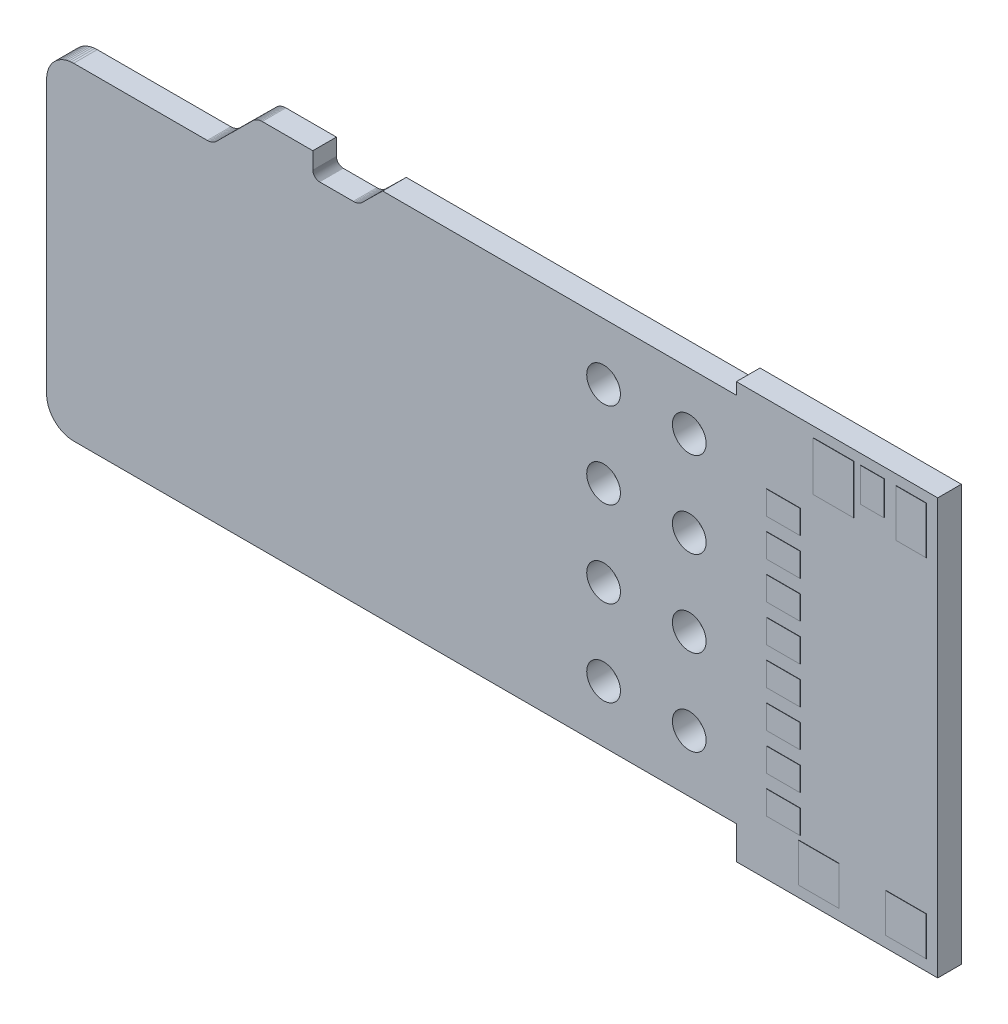
SolidWorks part; units mm, degrees
ref_plane "Front Plane" through (0, 0, 0) normal (0, 0, 1) x (1, 0, 0)
ref_plane "Top Plane" through (0, 0, 0) normal (0, 1, 0) x (1, 0, 0)
ref_plane "Right Plane" through (0, 0, 0) normal (1, 0, 0) x (0, 0, -1)
sketch "BOARD_OUTLINE" plane through (0, 0, 0) normal (0, 0, 1) x (1, 0, 0)
  line L0 (15, 5.5) -> (20.447, 5.5)
  line L1 (15, -5.5) -> (20.447, -5.5)
  line L2 (26.416, -6.477) -> (20.447, -6.477)
  line L3 (20.447, -5.5) -> (20.447, -6.477)
  line L4 (20.447, 5.85) -> (26.416, 5.85)
  line L5 (20.447, 5.85) -> (20.447, 5.5)
  line L6 (26.416, 5.85) -> (26.416, -6.477)
  line L7 (0, -4.7) -> (0, 3.4)
  line L8 (0, -4.7) -> (0.003, -4.7697)
  line L9 (0.003, -4.7697) -> (0.0122, -4.8389)
  line L10 (0.0122, -4.8389) -> (0.0273, -4.9071)
  line L11 (0.0273, -4.9071) -> (0.0482, -4.9736)
  line L12 (0.0482, -4.9736) -> (0.075, -5.0381)
  line L13 (0.075, -5.0381) -> (0.1072, -5.1)
  line L14 (0.1072, -5.1) -> (0.1447, -5.1589)
  line L15 (0.1447, -5.1589) -> (0.1872, -5.2142)
  line L16 (0.1872, -5.2142) -> (0.2343, -5.2657)
  line L17 (0.2343, -5.2657) -> (0.2858, -5.3128)
  line L18 (0.2858, -5.3128) -> (0.3411, -5.3553)
  line L19 (0.3411, -5.3553) -> (0.4, -5.3928)
  line L20 (0.4, -5.3928) -> (0.4619, -5.425)
  line L21 (0.4619, -5.425) -> (0.5264, -5.4518)
  line L22 (0.5264, -5.4518) -> (0.5929, -5.4727)
  line L23 (0.5929, -5.4727) -> (0.6611, -5.4878)
  line L24 (0.6611, -5.4878) -> (0.7303, -5.497)
  line L25 (0.7303, -5.497) -> (0.8, -5.5)
  line L26 (0.8, -5.5) -> (15, -5.5)
  line L27 (0.8, 4.2) -> (4.76, 4.2)
  line L28 (8.09, 4.8) -> (9.09, 4.8)
  line L29 (9.96, 5.5) -> (15, 5.5)
  line L30 (9.37, 4.92) -> (9.96, 5.5)
  line L31 (9.09, 4.8) -> (9.1245, 4.8018)
  line L32 (9.1245, 4.8018) -> (9.1587, 4.8067)
  line L33 (9.1587, 4.8067) -> (9.1923, 4.8145)
  line L34 (9.1923, 4.8145) -> (9.2251, 4.8252)
  line L35 (9.2251, 4.8252) -> (9.2569, 4.8387)
  line L36 (9.2569, 4.8387) -> (9.2873, 4.855)
  line L37 (9.2873, 4.855) -> (9.3163, 4.8738)
  line L38 (9.3163, 4.8738) -> (9.3434, 4.8951)
  line L39 (9.3434, 4.8951) -> (9.3687, 4.9186)
  line L40 (9.3687, 4.9186) -> (9.37, 4.92)
  line L41 (7.89, 5.5) -> (7.89, 5)
  line L42 (7.89, 5) -> (7.8912, 4.9822)
  line L43 (7.8912, 4.9822) -> (7.8939, 4.9646)
  line L44 (7.8939, 4.9646) -> (7.8981, 4.9473)
  line L45 (7.8981, 4.9473) -> (7.9038, 4.9304)
  line L46 (7.9038, 4.9304) -> (7.911, 4.914)
  line L47 (7.911, 4.914) -> (7.9196, 4.8984)
  line L48 (7.9196, 4.8984) -> (7.9295, 4.8836)
  line L49 (7.9295, 4.8836) -> (7.9406, 4.8697)
  line L50 (7.9406, 4.8697) -> (7.953, 4.8568)
  line L51 (7.953, 4.8568) -> (7.9664, 4.845)
  line L52 (7.9664, 4.845) -> (7.9807, 4.8344)
  line L53 (7.9807, 4.8344) -> (7.996, 4.8252)
  line L54 (7.996, 4.8252) -> (8.012, 4.8173)
  line L55 (8.012, 4.8173) -> (8.0286, 4.8108)
  line L56 (8.0286, 4.8108) -> (8.0457, 4.8058)
  line L57 (8.0457, 4.8058) -> (8.0632, 4.8023)
  line L58 (8.0632, 4.8023) -> (8.0809, 4.8004)
  line L59 (8.0809, 4.8004) -> (8.09, 4.8)
  line L60 (6.39, 5.5) -> (7.89, 5.5)
  line L61 (6.39, 5.5) -> (6.3551, 5.498)
  line L62 (6.3551, 5.498) -> (6.3206, 5.4929)
  line L63 (6.3206, 5.4929) -> (6.2866, 5.4849)
  line L64 (6.2866, 5.4849) -> (6.2535, 5.4739)
  line L65 (6.2535, 5.4739) -> (6.2214, 5.4601)
  line L66 (6.2214, 5.4601) -> (6.1907, 5.4435)
  line L67 (6.1907, 5.4435) -> (6.1615, 5.4243)
  line L68 (6.1615, 5.4243) -> (6.1341, 5.4027)
  line L69 (6.1341, 5.4027) -> (6.11, 5.38)
  line L70 (5.04, 4.32) -> (6.11, 5.38)
  line L71 (4.76, 4.2) -> (4.7951, 4.2021)
  line L72 (4.7951, 4.2021) -> (4.8299, 4.2073)
  line L73 (4.8299, 4.2073) -> (4.8641, 4.2155)
  line L74 (4.8641, 4.2155) -> (4.8974, 4.2267)
  line L75 (4.8974, 4.2267) -> (4.9296, 4.2407)
  line L76 (4.9296, 4.2407) -> (4.9605, 4.2575)
  line L77 (4.9605, 4.2575) -> (4.9899, 4.2769)
  line L78 (4.9899, 4.2769) -> (5.0174, 4.2988)
  line L79 (5.0174, 4.2988) -> (5.04, 4.32)
  line L80 (0.8, 4.2) -> (0.73, 4.1966)
  line L81 (0.73, 4.1966) -> (0.6605, 4.1872)
  line L82 (0.6605, 4.1872) -> (0.5921, 4.1717)
  line L83 (0.5921, 4.1717) -> (0.5254, 4.1503)
  line L84 (0.5254, 4.1503) -> (0.4607, 4.1232)
  line L85 (0.4607, 4.1232) -> (0.3987, 4.0905)
  line L86 (0.3987, 4.0905) -> (0.3397, 4.0526)
  line L87 (0.3397, 4.0526) -> (0.2843, 4.0097)
  line L88 (0.2843, 4.0097) -> (0.2328, 3.9621)
  line L89 (0.2328, 3.9621) -> (0.1857, 3.9102)
  line L90 (0.1857, 3.9102) -> (0.1433, 3.8543)
  line L91 (0.1433, 3.8543) -> (0.1059, 3.795)
  line L92 (0.1059, 3.795) -> (0.0738, 3.7327)
  line L93 (0.0738, 3.7327) -> (0.0472, 3.6678)
  line L94 (0.0472, 3.6678) -> (0.0264, 3.6009)
  line L95 (0.0264, 3.6009) -> (0.0116, 3.5323)
  line L96 (0.0116, 3.5323) -> (0.0027, 3.4628)
  line L97 (0.0027, 3.4628) -> (0, 3.4)
sketch "BOHRUNG" plane through (0, 0, 0) normal (0, 0, 1) x (1, 0, 0)
  circle A105 centre (16.51, -3.81) radius 0.5
  circle A106 centre (19.05, -3.81) radius 0.5
  circle A107 centre (16.51, -1.27) radius 0.5
  circle A108 centre (19.05, -1.27) radius 0.5
  circle A109 centre (16.51, 1.27) radius 0.5
  circle A110 centre (19.05, 1.27) radius 0.5
  circle A111 centre (16.51, 3.81) radius 0.5
  circle A112 centre (19.05, 3.81) radius 0.5
sketch "SOLDERMASK_BOTTOM" plane through (0, 0, 0) normal (0, 0, 1) x (1, 0, 0)
  line L0 (1.5, -4.9) -> (1.5, -4.1)
  line L1 (1.5, -4.1) -> (4.4, -4.1)
  line L2 (4.4, -4.1) -> (4.4, -4.9)
  line L3 (4.4, -4.9) -> (1.5, -4.9)
  line L4 (1.5, -3.8) -> (1.5, -3)
  line L5 (1.5, -3) -> (4.4, -3)
  line L6 (4.4, -3) -> (4.4, -3.8)
  line L7 (4.4, -3.8) -> (1.5, -3.8)
  line L8 (1.2, -2.7) -> (1.2, -1.9)
  line L9 (1.2, -1.9) -> (4.4, -1.9)
  line L10 (4.4, -1.9) -> (4.4, -2.7)
  line L11 (4.4, -2.7) -> (1.2, -2.7)
  line L12 (1.5, -1.6) -> (1.5, -0.8)
  line L13 (1.5, -0.8) -> (4.4, -0.8)
  line L14 (4.4, -0.8) -> (4.4, -1.6)
  line L15 (4.4, -1.6) -> (1.5, -1.6)
  line L16 (1.2, -0.5) -> (1.2, 0.3)
  line L17 (1.2, 0.3) -> (4.4, 0.3)
  line L18 (4.4, 0.3) -> (4.4, -0.5)
  line L19 (4.4, -0.5) -> (1.2, -0.5)
  line L20 (1.5, 0.6) -> (1.5, 1.4)
  line L21 (1.5, 1.4) -> (4.4, 1.4)
  line L22 (4.4, 1.4) -> (4.4, 0.6)
  line L23 (4.4, 0.6) -> (1.5, 0.6)
  line L24 (1.5, 1.7) -> (1.5, 2.5)
  line L25 (1.5, 2.5) -> (4.4, 2.5)
  line L26 (4.4, 2.5) -> (4.4, 1.7)
  line L27 (4.4, 1.7) -> (1.5, 1.7)
  line L28 (1.5, 2.8) -> (1.5, 3.6)
  line L29 (1.5, 3.6) -> (4.4, 3.6)
  line L30 (4.4, 3.6) -> (4.4, 2.8)
  line L31 (4.4, 2.8) -> (1.5, 2.8)
sketch "SOLDERMASK_TOP" plane through (0, 0, 0) normal (0, 0, 1) x (1, 0, 0)
  line L0 (23.494, -6.145) -> (22.294, -6.145)
  line L1 (22.294, -6.145) -> (22.294, -4.995)
  line L2 (22.294, -4.995) -> (23.494, -4.995)
  line L3 (23.494, -4.995) -> (23.494, -6.145)
  line L4 (26.084, -6.145) -> (24.884, -6.145)
  line L5 (24.884, -6.145) -> (24.884, -4.995)
  line L6 (24.884, -4.995) -> (26.084, -4.995)
  line L7 (26.084, -4.995) -> (26.084, -6.145)
  line L8 (21.344, -4.85) -> (21.344, -4.15)
  line L9 (21.344, -4.15) -> (22.344, -4.15)
  line L10 (22.344, -4.15) -> (22.344, -4.85)
  line L11 (22.344, -4.85) -> (21.344, -4.85)
  line L12 (21.344, -3.75) -> (21.344, -3.05)
  line L13 (21.344, -3.05) -> (22.344, -3.05)
  line L14 (22.344, -3.05) -> (22.344, -3.75)
  line L15 (22.344, -3.75) -> (21.344, -3.75)
  line L16 (21.344, -2.65) -> (21.344, -1.95)
  line L17 (21.344, -1.95) -> (22.344, -1.95)
  line L18 (22.344, -1.95) -> (22.344, -2.65)
  line L19 (22.344, -2.65) -> (21.344, -2.65)
  line L20 (21.344, -1.55) -> (21.344, -0.85)
  line L21 (21.344, -0.85) -> (22.344, -0.85)
  line L22 (22.344, -0.85) -> (22.344, -1.55)
  line L23 (22.344, -1.55) -> (21.344, -1.55)
  line L24 (21.344, -0.45) -> (21.344, 0.25)
  line L25 (21.344, 0.25) -> (22.344, 0.25)
  line L26 (22.344, 0.25) -> (22.344, -0.45)
  line L27 (22.344, -0.45) -> (21.344, -0.45)
  line L28 (21.344, 0.65) -> (21.344, 1.35)
  line L29 (21.344, 1.35) -> (22.344, 1.35)
  line L30 (22.344, 1.35) -> (22.344, 0.65)
  line L31 (22.344, 0.65) -> (21.344, 0.65)
  line L32 (21.344, 1.75) -> (21.344, 2.45)
  line L33 (21.344, 2.45) -> (22.344, 2.45)
  line L34 (22.344, 2.45) -> (22.344, 1.75)
  line L35 (22.344, 1.75) -> (21.344, 1.75)
  line L36 (21.344, 2.85) -> (21.344, 3.55)
  line L37 (21.344, 3.55) -> (22.344, 3.55)
  line L38 (22.344, 3.55) -> (22.344, 2.85)
  line L39 (22.344, 2.85) -> (21.344, 2.85)
  line L40 (23.934, 4.1) -> (22.734, 4.1)
  line L41 (22.734, 4.1) -> (22.734, 5.55)
  line L42 (22.734, 5.55) -> (23.934, 5.55)
  line L43 (23.934, 5.55) -> (23.934, 4.1)
  line L44 (26.084, 4.15) -> (25.184, 4.15)
  line L45 (25.184, 4.15) -> (25.184, 5.55)
  line L46 (25.184, 5.55) -> (26.084, 5.55)
  line L47 (26.084, 5.55) -> (26.084, 4.15)
  line L48 (24.834, 4.55) -> (24.134, 4.55)
  line L49 (24.134, 4.55) -> (24.134, 5.55)
  line L50 (24.134, 5.55) -> (24.834, 5.55)
  line L51 (24.834, 5.55) -> (24.834, 4.55)
extrude "Aufsatz-Linear austragen1" add sketch "BOARD_OUTLINE" along normal blind 0.7
extrude "Aufsatz-Linear austragen2" add sketch "SOLDERMASK_BOTTOM" against normal blind 0.01 from surface at 0 starting at face at (5.5038, 2.3742, 0)
extrude "Aufsatz-Linear austragen3" add sketch "SOLDERMASK_TOP" along normal blind 0.01 from surface at 0.7 starting at face at (5.5038, 2.3742, 0.7)
extrude "Schnitt-Linear austragen1" cut sketch "BOHRUNG" against normal through all both and the other way through all
